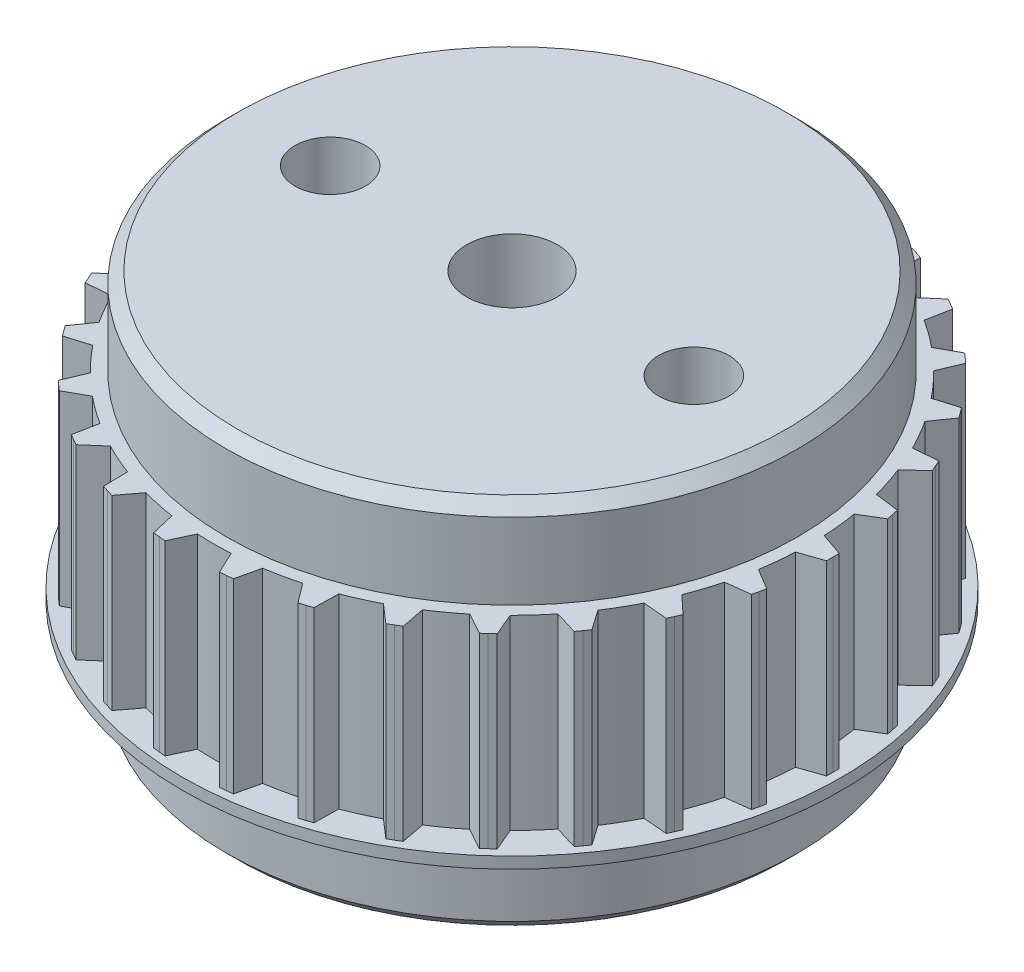
SolidWorks part; units mm, degrees
ref_plane "Front Plane" through (0, 0, 0) normal (0, 0, 1) x (1, 0, 0)
ref_plane "Top Plane" through (0, 0, 0) normal (0, 1, 0) x (1, 0, 0)
ref_plane "Right Plane" through (0, 0, 0) normal (1, 0, 0) x (0, 0, -1)
sketch "Sketch1" plane through (0, 0, 0) normal (0, 1, 0) x (1, 0, 0)
  line L0 (0, 0) -> (-13.12, 0) construction
  line L1 (-13.12, 0) -> (-15.3941, 0) construction
  line L4 (-14.12, 0) -> (-14.1172, 0.28)
  line L5 (-14.1172, 0.28) -> (-13.1049, 0.63)
  line L6 (-14.12, 0) -> (-14.1172, -0.28)
  line L7 (-14.1172, -0.28) -> (-13.1049, -0.63)
  line L8 (-13.7505, 3.209) -> (-12.6875, 3.3409)
  line L9 (-13.8669, 2.6613) -> (-12.9495, 2.1084)
  line L10 (-13.8114, 2.9357) -> (-13.8669, 2.6613)
  line L11 (-13.8114, 2.9357) -> (-13.7505, 3.209)
  line L12 (-12.7828, 5.9978) -> (-11.7156, 5.9058)
  line L13 (-13.0106, 5.4862) -> (-12.2281, 4.7547)
  line L14 (-12.8993, 5.7431) -> (-13.0106, 5.4862)
  line L15 (-12.8993, 5.7431) -> (-12.7828, 5.9978)
  line L16 (-11.2565, 8.5244) -> (-10.2318, 8.2125)
  line L17 (-11.5857, 8.0714) -> (-10.9724, 7.1932)
  line L18 (-11.4233, 8.2995) -> (-11.5857, 8.0714)
  line L19 (-11.4233, 8.2995) -> (-11.2565, 8.5244)
  line L20 (-9.2382, 10.6785) -> (-8.3007, 10.1604)
  line L21 (-9.6543, 10.3038) -> (-9.237, 9.3173)
  line L22 (-9.4481, 10.4932) -> (-9.6543, 10.3038)
  line L23 (-9.4481, 10.4932) -> (-9.2382, 10.6785)
  line L24 (-6.8161, 12.3659) -> (-6.0068, 11.6641)
  line L25 (-7.3011, 12.0859) -> (-7.098, 11.0341)
  line L26 (-7.06, 12.2283) -> (-7.3011, 12.0859)
  line L27 (-7.06, 12.2283) -> (-6.8161, 12.3659)
  line L28 (-4.0962, 13.5128) -> (-3.4505, 12.6581)
  line L29 (-4.6288, 13.3398) -> (-4.6488, 12.2688)
  line L30 (-4.3633, 13.4289) -> (-4.6288, 13.3398)
  line L31 (-4.3633, 13.4289) -> (-4.0962, 13.5128)
  line L32 (-1.1972, 14.0692) -> (-0.7433, 13.0989)
  line L33 (-1.7541, 14.0106) -> (-1.9964, 12.9672)
  line L34 (-1.4759, 14.0426) -> (-1.7541, 14.0106)
  line L35 (-1.4759, 14.0426) -> (-1.1972, 14.0692)
  line L36 (1.7541, 14.0106) -> (1.9964, 12.9672)
  line L37 (1.1972, 14.0692) -> (0.7433, 13.0989)
  line L38 (1.4759, 14.0426) -> (1.1972, 14.0692)
  line L39 (1.4759, 14.0426) -> (1.7541, 14.0106)
  line L40 (4.6287, 13.3398) -> (4.6488, 12.2688)
  line L41 (4.0962, 13.5128) -> (3.4505, 12.6581)
  line L42 (4.3633, 13.4289) -> (4.0962, 13.5128)
  line L43 (4.3633, 13.4289) -> (4.6287, 13.3398)
  line L44 (7.3011, 12.0859) -> (7.098, 11.0341)
  line L45 (6.8161, 12.3659) -> (6.0068, 11.6641)
  line L46 (7.06, 12.2283) -> (6.8161, 12.3659)
  line L47 (7.06, 12.2283) -> (7.3011, 12.0859)
  line L48 (9.6543, 10.3038) -> (9.237, 9.3173)
  line L49 (9.2382, 10.6785) -> (8.3007, 10.1604)
  line L50 (9.4481, 10.4932) -> (9.2382, 10.6785)
  line L51 (9.4481, 10.4932) -> (9.6543, 10.3038)
  line L52 (11.5856, 8.0714) -> (10.9724, 7.1932)
  line L53 (11.2565, 8.5244) -> (10.2318, 8.2125)
  line L54 (11.4233, 8.2995) -> (11.2565, 8.5244)
  line L55 (11.4233, 8.2995) -> (11.5856, 8.0714)
  line L56 (13.0106, 5.4862) -> (12.2281, 4.7547)
  line L57 (12.7828, 5.9978) -> (11.7156, 5.9058)
  line L58 (12.8993, 5.7431) -> (12.7828, 5.9978)
  line L59 (12.8993, 5.7431) -> (13.0106, 5.4862)
  line L60 (13.8669, 2.6613) -> (12.9495, 2.1084)
  line L61 (13.7505, 3.209) -> (12.6875, 3.3409)
  line L62 (13.8114, 2.9357) -> (13.7505, 3.209)
  line L63 (13.8114, 2.9357) -> (13.8669, 2.6613)
  line L64 (14.1172, -0.28) -> (13.1049, -0.63)
  line L65 (14.1172, 0.28) -> (13.1049, 0.63)
  line L66 (14.12, 0) -> (14.1172, 0.28)
  line L67 (14.12, 0) -> (14.1172, -0.28)
  line L68 (13.7505, -3.209) -> (12.6875, -3.3409)
  line L69 (13.8669, -2.6613) -> (12.9495, -2.1084)
  line L70 (13.8114, -2.9357) -> (13.8669, -2.6613)
  line L71 (13.8114, -2.9357) -> (13.7505, -3.209)
  line L72 (12.7828, -5.9978) -> (11.7156, -5.9058)
  line L73 (13.0106, -5.4862) -> (12.2281, -4.7547)
  line L74 (12.8993, -5.7431) -> (13.0106, -5.4862)
  line L75 (12.8993, -5.7431) -> (12.7828, -5.9978)
  line L76 (11.2565, -8.5244) -> (10.2318, -8.2125)
  line L77 (11.5857, -8.0714) -> (10.9724, -7.1932)
  line L78 (11.4233, -8.2995) -> (11.5857, -8.0714)
  line L79 (11.4233, -8.2995) -> (11.2565, -8.5244)
  line L80 (9.2382, -10.6785) -> (8.3007, -10.1604)
  line L81 (9.6543, -10.3038) -> (9.237, -9.3173)
  line L82 (9.4481, -10.4932) -> (9.6543, -10.3038)
  line L83 (9.4481, -10.4932) -> (9.2382, -10.6785)
  line L84 (6.8161, -12.3659) -> (6.0068, -11.6641)
  line L85 (7.3011, -12.0859) -> (7.098, -11.0341)
  line L86 (7.06, -12.2283) -> (7.3011, -12.0859)
  line L87 (7.06, -12.2283) -> (6.8161, -12.3659)
  line L88 (4.0962, -13.5128) -> (3.4505, -12.6581)
  line L89 (4.6288, -13.3398) -> (4.6488, -12.2688)
  line L90 (4.3633, -13.4289) -> (4.6288, -13.3398)
  line L91 (4.3633, -13.4289) -> (4.0962, -13.5128)
  line L92 (1.1972, -14.0692) -> (0.7433, -13.0989)
  line L93 (1.7541, -14.0106) -> (1.9964, -12.9672)
  line L94 (1.4759, -14.0426) -> (1.7541, -14.0106)
  line L95 (1.4759, -14.0426) -> (1.1972, -14.0692)
  line L96 (-1.7541, -14.0106) -> (-1.9964, -12.9672)
  line L97 (-1.1972, -14.0692) -> (-0.7433, -13.0989)
  line L98 (-1.4759, -14.0426) -> (-1.1972, -14.0692)
  line L99 (-1.4759, -14.0426) -> (-1.7541, -14.0106)
  line L100 (-4.6287, -13.3398) -> (-4.6488, -12.2688)
  line L101 (-4.0962, -13.5128) -> (-3.4505, -12.6581)
  line L102 (-4.3633, -13.4289) -> (-4.0962, -13.5128)
  line L103 (-4.3633, -13.4289) -> (-4.6287, -13.3398)
  line L104 (-7.3011, -12.0859) -> (-7.098, -11.0341)
  line L105 (-6.8161, -12.3659) -> (-6.0068, -11.6641)
  line L106 (-7.06, -12.2283) -> (-6.8161, -12.3659)
  line L107 (-7.06, -12.2283) -> (-7.3011, -12.0859)
  line L108 (-9.6543, -10.3038) -> (-9.237, -9.3173)
  line L109 (-9.2382, -10.6785) -> (-8.3007, -10.1604)
  line L110 (-9.4481, -10.4932) -> (-9.2382, -10.6785)
  line L111 (-9.4481, -10.4932) -> (-9.6543, -10.3038)
  line L112 (-11.5856, -8.0714) -> (-10.9724, -7.1932)
  line L113 (-11.2565, -8.5244) -> (-10.2318, -8.2125)
  line L114 (-11.4233, -8.2995) -> (-11.2565, -8.5244)
  line L115 (-11.4233, -8.2995) -> (-11.5856, -8.0714)
  line L116 (-13.0106, -5.4862) -> (-12.2281, -4.7547)
  line L117 (-12.7828, -5.9978) -> (-11.7156, -5.9058)
  line L118 (-12.8993, -5.7431) -> (-12.7828, -5.9978)
  line L119 (-12.8993, -5.7431) -> (-13.0106, -5.4862)
  line L120 (-13.8669, -2.6613) -> (-12.9495, -2.1084)
  line L121 (-13.7505, -3.209) -> (-12.6875, -3.3409)
  line L122 (-13.8114, -2.9357) -> (-13.7505, -3.209)
  line L123 (-13.8114, -2.9357) -> (-13.8669, -2.6613)
  circle A0 centre (0, 0) radius 13.12
  circle A2 centre (0, 0) radius 13.12
  circle A3 centre (0, 0) radius 13.12
  circle A4 centre (0, 0) radius 13.12
  circle A5 centre (0, 0) radius 13.12
  circle A6 centre (0, 0) radius 13.12
  circle A7 centre (0, 0) radius 13.12
  circle A8 centre (0, 0) radius 13.12
  circle A9 centre (0, 0) radius 13.12
  circle A10 centre (0, 0) radius 13.12
  circle A11 centre (0, 0) radius 13.12
  circle A12 centre (0, 0) radius 13.12
  circle A13 centre (0, 0) radius 13.12
  circle A14 centre (0, 0) radius 13.12
  circle A15 centre (0, 0) radius 13.12
  circle A16 centre (0, 0) radius 13.12
  circle A17 centre (0, 0) radius 13.12
  circle A18 centre (0, 0) radius 13.12
  circle A19 centre (0, 0) radius 13.12
  circle A20 centre (0, 0) radius 13.12
  circle A21 centre (0, 0) radius 13.12
  circle A22 centre (0, 0) radius 13.12
  circle A23 centre (0, 0) radius 13.12
  circle A24 centre (0, 0) radius 13.12
  circle A25 centre (0, 0) radius 13.12
  circle A26 centre (0, 0) radius 13.12
  circle A27 centre (0, 0) radius 13.12
  circle A28 centre (0, 0) radius 13.12
  circle A29 centre (0, 0) radius 13.12
  circle A30 centre (0, 0) radius 13.12
  point P187 (0, 0)
  dimension "D1" = 26.24
  dimension "D3" = 0.63
  dimension "D4" = 0.63
  dimension "D5" = 0.28
  dimension "D6" = 0.28
  dimension "D2" = 30
sketch "Sketch3" plane through (0, 0, 0) normal (0, 1, 0) x (1, 0, 0)
  circle A0 centre (0, 0) radius 13.12
extrude "Boss-Extrude1" add sketch "Sketch3" along normal blind 8.2
sketch "Sketch4" plane through (0, 0, 0) normal (0, 1, 0) x (1, 0, 0)
  line L0 (-14.1172, -0.28) -> (-13.1049, -0.63) construction
  line L1 (-14.12, 0) -> (-14.1172, -0.28) construction
  line L2 (-14.12, 0) -> (-14.1172, 0.28) construction
  line L3 (-14.1172, 0.28) -> (-13.1049, 0.63) construction
  line L4 (-14.1172, -0.28) -> (-12.8499, -0.7181)
  line L5 (-14.12, 0) -> (-14.1172, -0.28)
  line L6 (-14.12, 0) -> (-14.1172, 0.28)
  line L7 (-14.1172, 0.28) -> (-12.8499, 0.7181)
  line L8 (-13.8669, 2.6613) -> (-12.7185, 1.9692)
  line L9 (-13.8114, 2.9357) -> (-13.8669, 2.6613)
  line L10 (-13.8114, 2.9357) -> (-13.7505, 3.209)
  line L11 (-13.7505, 3.209) -> (-12.4198, 3.3741)
  line L12 (-13.0106, 5.4862) -> (-12.0311, 4.5705)
  line L13 (-12.8993, 5.7431) -> (-13.0106, 5.4862)
  line L14 (-12.8993, 5.7431) -> (-12.7828, 5.9978)
  line L15 (-12.7828, 5.9978) -> (-11.4469, 5.8826)
  line L16 (-11.5857, 8.0714) -> (-10.8179, 6.972)
  line L17 (-11.4233, 8.2995) -> (-11.5857, 8.0714)
  line L18 (-11.4233, 8.2995) -> (-11.2565, 8.5244)
  line L19 (-11.2565, 8.5244) -> (-9.9737, 8.134)
  line L20 (-9.6543, 10.3038) -> (-9.132, 9.0688)
  line L21 (-9.4481, 10.4932) -> (-9.6543, 10.3038)
  line L22 (-9.4481, 10.4932) -> (-9.2382, 10.6785)
  line L23 (-9.2382, 10.6785) -> (-8.0646, 10.0299)
  line L24 (-7.3011, 12.0859) -> (-7.0469, 10.7693)
  line L25 (-7.06, 12.2283) -> (-7.3011, 12.0859)
  line L26 (-7.06, 12.2283) -> (-6.8161, 12.3659)
  line L27 (-6.8161, 12.3659) -> (-5.8031, 11.4874)
  line L28 (-4.6288, 13.3398) -> (-4.6538, 11.9991)
  line L29 (-4.3633, 13.4289) -> (-4.6288, 13.3398)
  line L30 (-4.3633, 13.4289) -> (-4.0962, 13.5128)
  line L31 (-4.0962, 13.5128) -> (-3.2879, 12.4429)
  line L32 (-1.7541, 14.0106) -> (-2.0574, 12.7045)
  line L33 (-1.4759, 14.0426) -> (-1.7541, 14.0106)
  line L34 (-1.4759, 14.0426) -> (-1.1972, 14.0692)
  line L35 (-1.1972, 14.0692) -> (-0.629, 12.8546)
  line L36 (1.1972, 14.0692) -> (0.629, 12.8546)
  line L37 (1.4759, 14.0426) -> (1.1972, 14.0692)
  line L38 (1.4759, 14.0426) -> (1.7541, 14.0106)
  line L39 (1.7541, 14.0106) -> (2.0574, 12.7045)
  line L40 (4.0962, 13.5128) -> (3.2879, 12.4429)
  line L41 (4.3633, 13.4289) -> (4.0962, 13.5128)
  line L42 (4.3633, 13.4289) -> (4.6287, 13.3398)
  line L43 (4.6287, 13.3398) -> (4.6538, 11.9991)
  line L44 (6.8161, 12.3659) -> (5.8031, 11.4874)
  line L45 (7.06, 12.2283) -> (6.8161, 12.3659)
  line L46 (7.06, 12.2283) -> (7.3011, 12.0859)
  line L47 (7.3011, 12.0859) -> (7.0469, 10.7693)
  line L48 (9.2382, 10.6785) -> (8.0646, 10.0299)
  line L49 (9.4481, 10.4932) -> (9.2382, 10.6785)
  line L50 (9.4481, 10.4932) -> (9.6543, 10.3038)
  line L51 (9.6543, 10.3038) -> (9.132, 9.0688)
  line L52 (11.2565, 8.5244) -> (9.9737, 8.134)
  line L53 (11.4233, 8.2995) -> (11.2565, 8.5244)
  line L54 (11.4233, 8.2995) -> (11.5856, 8.0714)
  line L55 (11.5856, 8.0714) -> (10.8179, 6.972)
  line L56 (12.7828, 5.9978) -> (11.4469, 5.8826)
  line L57 (12.8993, 5.7431) -> (12.7828, 5.9978)
  line L58 (12.8993, 5.7431) -> (13.0106, 5.4862)
  line L59 (13.0106, 5.4862) -> (12.0311, 4.5705)
  line L60 (13.7505, 3.209) -> (12.4198, 3.3741)
  line L61 (13.8114, 2.9357) -> (13.7505, 3.209)
  line L62 (13.8114, 2.9357) -> (13.8669, 2.6613)
  line L63 (13.8669, 2.6613) -> (12.7185, 1.9692)
  line L64 (14.1172, 0.28) -> (12.8499, 0.7181)
  line L65 (14.12, 0) -> (14.1172, 0.28)
  line L66 (14.12, 0) -> (14.1172, -0.28)
  line L67 (14.1172, -0.28) -> (12.8499, -0.7181)
  line L68 (13.8669, -2.6613) -> (12.7185, -1.9692)
  line L69 (13.8114, -2.9357) -> (13.8669, -2.6613)
  line L70 (13.8114, -2.9357) -> (13.7505, -3.209)
  line L71 (13.7505, -3.209) -> (12.4198, -3.3741)
  line L72 (13.0106, -5.4862) -> (12.0311, -4.5705)
  line L73 (12.8993, -5.7431) -> (13.0106, -5.4862)
  line L74 (12.8993, -5.7431) -> (12.7828, -5.9978)
  line L75 (12.7828, -5.9978) -> (11.4469, -5.8826)
  line L76 (11.5857, -8.0714) -> (10.8179, -6.972)
  line L77 (11.4233, -8.2995) -> (11.5857, -8.0714)
  line L78 (11.4233, -8.2995) -> (11.2565, -8.5244)
  line L79 (11.2565, -8.5244) -> (9.9737, -8.134)
  line L80 (9.6543, -10.3038) -> (9.132, -9.0688)
  line L81 (9.4481, -10.4932) -> (9.6543, -10.3038)
  line L82 (9.4481, -10.4932) -> (9.2382, -10.6785)
  line L83 (9.2382, -10.6785) -> (8.0646, -10.0299)
  line L84 (7.3011, -12.0859) -> (7.0469, -10.7693)
  line L85 (7.06, -12.2283) -> (7.3011, -12.0859)
  line L86 (7.06, -12.2283) -> (6.8161, -12.3659)
  line L87 (6.8161, -12.3659) -> (5.8031, -11.4874)
  line L88 (4.6288, -13.3398) -> (4.6538, -11.9991)
  line L89 (4.3633, -13.4289) -> (4.6288, -13.3398)
  line L90 (4.3633, -13.4289) -> (4.0962, -13.5128)
  line L91 (4.0962, -13.5128) -> (3.2879, -12.4429)
  line L92 (1.7541, -14.0106) -> (2.0574, -12.7045)
  line L93 (1.4759, -14.0426) -> (1.7541, -14.0106)
  line L94 (1.4759, -14.0426) -> (1.1972, -14.0692)
  line L95 (1.1972, -14.0692) -> (0.629, -12.8546)
  line L96 (-1.1972, -14.0692) -> (-0.629, -12.8546)
  line L97 (-1.4759, -14.0426) -> (-1.1972, -14.0692)
  line L98 (-1.4759, -14.0426) -> (-1.7541, -14.0106)
  line L99 (-1.7541, -14.0106) -> (-2.0574, -12.7045)
  line L100 (-4.0962, -13.5128) -> (-3.2879, -12.4429)
  line L101 (-4.3633, -13.4289) -> (-4.0962, -13.5128)
  line L102 (-4.3633, -13.4289) -> (-4.6287, -13.3398)
  line L103 (-4.6287, -13.3398) -> (-4.6538, -11.9991)
  line L104 (-6.8161, -12.3659) -> (-5.8031, -11.4874)
  line L105 (-7.06, -12.2283) -> (-6.8161, -12.3659)
  line L106 (-7.06, -12.2283) -> (-7.3011, -12.0859)
  line L107 (-7.3011, -12.0859) -> (-7.0469, -10.7693)
  line L108 (-9.2382, -10.6785) -> (-8.0646, -10.0299)
  line L109 (-9.4481, -10.4932) -> (-9.2382, -10.6785)
  line L110 (-9.4481, -10.4932) -> (-9.6543, -10.3038)
  line L111 (-9.6543, -10.3038) -> (-9.132, -9.0688)
  line L112 (-11.2565, -8.5244) -> (-9.9737, -8.134)
  line L113 (-11.4233, -8.2995) -> (-11.2565, -8.5244)
  line L114 (-11.4233, -8.2995) -> (-11.5856, -8.0714)
  line L115 (-11.5856, -8.0714) -> (-10.8179, -6.972)
  line L116 (-12.7828, -5.9978) -> (-11.4469, -5.8826)
  line L117 (-12.8993, -5.7431) -> (-12.7828, -5.9978)
  line L118 (-12.8993, -5.7431) -> (-13.0106, -5.4862)
  line L119 (-13.0106, -5.4862) -> (-12.0311, -4.5705)
  line L120 (-13.7505, -3.209) -> (-12.4198, -3.3741)
  line L121 (-13.8114, -2.9357) -> (-13.7505, -3.209)
  line L122 (-13.8114, -2.9357) -> (-13.8669, -2.6613)
  line L123 (-13.8669, -2.6613) -> (-12.7185, -1.9692)
  arc A1 (-12.4198, 3.3741) -> (-12.7185, 1.9692) centre (0, 0) ccw
  circle A2 centre (0, 0) radius 12.87
  arc A3 (-12.8499, 0.7181) -> (-12.8499, -0.7181) centre (0, 0) ccw
  arc A4 (-11.4469, 5.8826) -> (-12.0311, 4.5705) centre (0, 0) ccw
  arc A5 (-9.9737, 8.134) -> (-10.8179, 6.972) centre (0, 0) ccw
  arc A6 (-8.0646, 10.0299) -> (-9.132, 9.0688) centre (0, 0) ccw
  arc A7 (-5.8031, 11.4874) -> (-7.0469, 10.7693) centre (0, 0) ccw
  arc A8 (-3.2879, 12.4429) -> (-4.6538, 11.9991) centre (0, 0) ccw
  arc A9 (-0.629, 12.8546) -> (-2.0574, 12.7045) centre (0, 0) ccw
  arc A10 (2.0574, 12.7045) -> (0.629, 12.8546) centre (0, 0) ccw
  arc A11 (4.6538, 11.9991) -> (3.2879, 12.4429) centre (0, 0) ccw
  arc A12 (7.0469, 10.7693) -> (5.8031, 11.4874) centre (0, 0) ccw
  arc A13 (9.132, 9.0688) -> (8.0646, 10.0299) centre (0, 0) ccw
  arc A14 (10.8179, 6.972) -> (9.9737, 8.134) centre (0, 0) ccw
  arc A15 (12.0311, 4.5705) -> (11.4469, 5.8826) centre (0, 0) ccw
  arc A16 (12.7185, 1.9692) -> (12.4198, 3.3741) centre (0, 0) ccw
  arc A17 (12.8499, -0.7181) -> (12.8499, 0.7181) centre (0, 0) ccw
  arc A18 (12.4198, -3.3741) -> (12.7185, -1.9692) centre (0, 0) ccw
  arc A19 (11.4469, -5.8826) -> (12.0311, -4.5705) centre (0, 0) ccw
  arc A20 (9.9737, -8.134) -> (10.8179, -6.972) centre (0, 0) ccw
  arc A21 (8.0646, -10.0299) -> (9.132, -9.0688) centre (0, 0) ccw
  arc A22 (5.8031, -11.4874) -> (7.0469, -10.7693) centre (0, 0) ccw
  arc A23 (3.2879, -12.4429) -> (4.6538, -11.9991) centre (0, 0) ccw
  arc A24 (0.629, -12.8546) -> (2.0574, -12.7045) centre (0, 0) ccw
  arc A25 (-2.0574, -12.7045) -> (-0.629, -12.8546) centre (0, 0) ccw
  arc A26 (-4.6538, -11.9991) -> (-3.2879, -12.4429) centre (0, 0) ccw
  arc A27 (-7.0469, -10.7693) -> (-5.8031, -11.4874) centre (0, 0) ccw
  arc A28 (-9.132, -9.0688) -> (-8.0646, -10.0299) centre (0, 0) ccw
  arc A29 (-10.8179, -6.972) -> (-9.9737, -8.134) centre (0, 0) ccw
  arc A30 (-12.0311, -4.5705) -> (-11.4469, -5.8826) centre (0, 0) ccw
  arc A31 (-12.7185, -1.9692) -> (-12.4198, -3.3741) centre (0, 0) ccw
  point P156 (0, 0)
  dimension "D1" = 0.25
  dimension "D2" = 30
extrude "Boss-Extrude2" add sketch "Sketch4" along normal up to surface (8.2 mm away) up to face at (0, 8.2, 13.12)
sketch "Sketch5" plane through (0, 0, 0) normal (0, -1, 0) x (1, 0, 0)
  circle A0 centre (0, 0) radius 14.5
  dimension "D1" = 29
extrude "Boss-Extrude3" add sketch "Sketch5" along normal blind 0.5
sketch "Sketch6" plane through (0, -0.5, 0) normal (0, -1, 0) x (-1, 0, 0)
  circle A0 centre (0, 0) radius 12.575
  dimension "D1" = 25.15
extrude "Boss-Extrude4" add sketch "Sketch6" along normal blind 3.85
sketch "Sketch7" plane through (0, 8.2, 0) normal (0, 1, 0) x (1, 0, 0)
  circle A0 centre (0, 0) radius 12.575
  dimension "D1" = 25.15
extrude "Boss-Extrude5" add sketch "Sketch7" along normal blind 3.85
chamfer "Chamfer1" distance 0.5 angle 45 2 edges at (0, -4.35, -12.575) (0, 12.05, 12.575)
sketch "Sketch8" plane through (0, 12.05, 0) normal (0, 1, 0) x (1, 0, 0)
  line L1 (5, -9) -> (-5, -9)
  line L2 (5, -9) -> (5, 9)
  line L3 (5, 9) -> (-5, 9)
  line L4 (-5, -9) -> (-5, 9)
  line L5 (5, -9) -> (-5, 9) construction
  line L6 (5, 9) -> (-5, -9) construction
  point P0 (0, 0)
  dimension "D1" = 10
  dimension "D2" = 18
extrude "Cut-Extrude1" cut sketch "Sketch8" against normal through all both and the other way through all
sketch "Sketch9" plane through (0, 12.05, 0) normal (0, 1, 0) x (1, 0, 0)
  line L0 (0, 0) -> (-8, 0) construction
  line L1 (0, 0) -> (8, 0) construction
  circle A0 centre (-8, 0) radius 1.55
  circle A1 centre (8, 0) radius 1.55
  dimension "D3" = 3.1
  dimension "D4" = 3.1
  dimension "D1" = 8
  dimension "D2" = 8
extrude "Cut-Extrude2" cut sketch "Sketch9" against normal through all both
fillet "Fillet1" radius 1 4 edges at (-5, 3.85, 9) (5, 3.85, 9) (5, 3.85, -9) (-5, 3.85, -9)
sketch "Sketch10" plane through (0, -4.35, 0) normal (0, -1, 0) x (1, 0, 0)
  line L1 (6.0073, -9.657) -> (-6.0073, -9.657)
  line L2 (6.0073, -9.657) -> (6.0073, 9.657)
  line L3 (6.0073, 9.657) -> (-6.0073, 9.657)
  line L4 (-6.0073, -9.657) -> (-6.0073, 9.657)
  line L5 (6.0073, -9.657) -> (-6.0073, 9.657) construction
  line L6 (6.0073, 9.657) -> (-6.0073, -9.657) construction
  circle A0 centre (0, 0) radius 1.995
  dimension "D1" = 3.99
extrude "Boss-Extrude6" add sketch "Sketch10" against normal up to surface (16.4 mm away) up to face at (-8, 12.05, 1.55)
